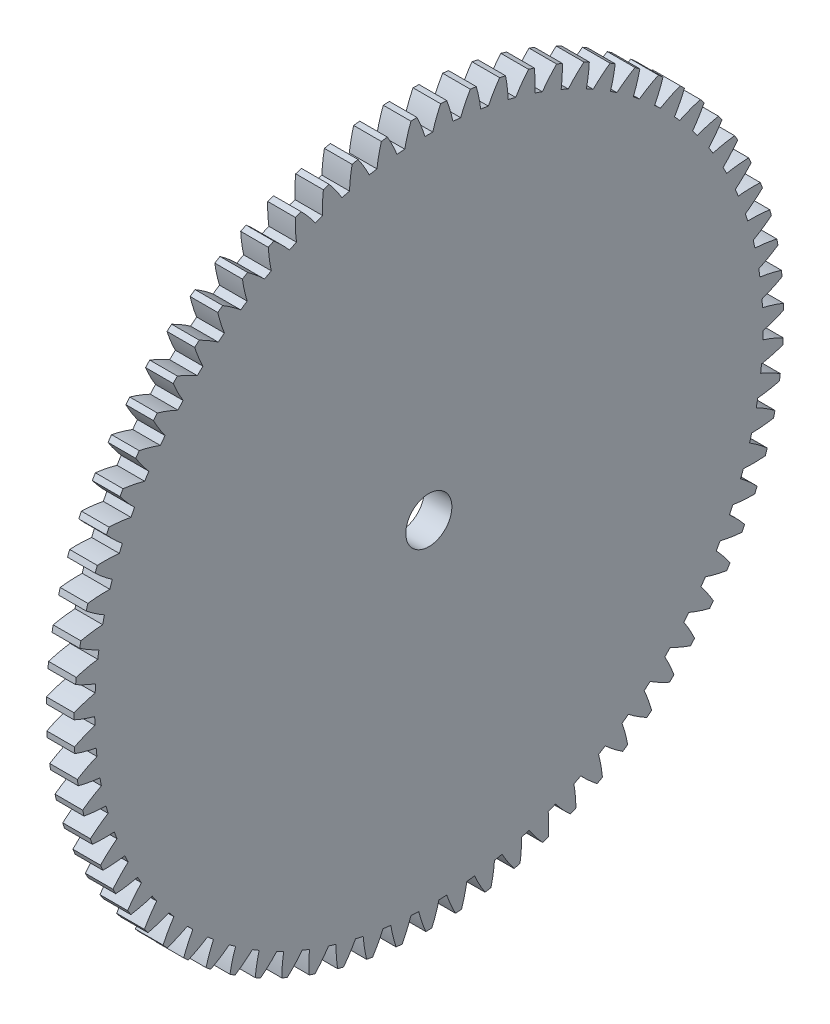
SolidWorks part; units mm, degrees
ref_plane "Plane1" through (0, 0, 0) normal (0, 0, 1) x (1, 0, 0)
ref_plane "Plane2" through (0, 0, 0) normal (0, 1, 0) x (1, 0, 0)
ref_plane "Plane3" through (0, 0, 0) normal (1, 0, 0) x (0, 0, -1)
sketch "HoldingSke" plane through (0, 0, 0) normal (0, 1, 0) x (1, 0, 0)
  line L0 (0, 0) -> (0.2588, -0.9659)
  line L1 (-15, 0) -> (100, 0) construction
  line L2 (0, 0) -> (-2.1039, 2.3779)
  line L3 (0, 0) -> (-11.863, 4.5341)
  line L4 (0, 0) -> (2.2352, 8.3417)
  line L5 (0, 0) -> (-46.8476, -17.4728)
  line L6 (0, 0) -> (-2.4869, -1.6779)
  line L7 (-2.1039, 2.3779) -> (8.6586, 51.2059)
  line L8 (-76.2, 54.61) -> (-75.3, 54.61)
  line L9 (-71.009, 38.7566) -> (-53.1078, 45.2721)
  line L10 (-76.2, 71.12) -> (104.1128, 71.12)
  line L11 (0, 0) -> (-3, 0)
  line L12 (-76.2, 101.6) -> (-76.162, 101.6)
  line L13 (24.9733, 27.94) -> (52.9518, 28.4284)
  line L14 (24.9733, 27.94) -> (24.9743, 27.94)
  line L15 (24.9733, 27.94) -> (100.4006, 29.5858)
  line L16 (-63.627, -1) -> (-12.827, -1)
  circle A0 centre (0, 0) radius 2.5
  circle A1 centre (0, 0) radius 36.249
  circle A2 centre (0, 0) radius 37.5
  circle A3 centre (0, 0) radius 2.5
  dimension "MHD" = 72.498
  dimension "Hub_dia" = 75
  dimension "Bore" = 5
  dimension "MBD" = 5
  dimension "Num_teeth" = 75
  dimension "Pitch_radius" = 180.3128
  dimension "Pitch" = 1
  dimension "Width" = 3
  dimension "Overall_len" = 50
  dimension "Show_teeth" = 75
  dimension "Thickness" = 3
  dimension "OAL" = 50.0001
  dimension "T_dim" = 0.9
  dimension "Ap" = 20
  dimension "H" = 19.05
  dimension "Backlash" = 0.038
  dimension "Addendum_fac" = 1
  dimension "Dedendum_fac" = 1.25
  dimension "Clearance_fac" = 0.25
  dimension "Dedendum_add" = 0.001
  dimension "Module" = 1
sketch "BasProSke" plane through (0, 0, 0) normal (0, 1, 0) x (1, 0, 0)
  line L0 (-10, 0) -> (60, 0) construction
  line L1 (0, 0) -> (0, 38.5)
  line L2 (0, 0) -> (3, 0)
  line L3 (3, 0) -> (3, 38.5)
  line L4 (3, 38.5) -> (0, 38.5)
  dimension "Diameter" = 77
  dimension "Thickness" = 3
revolve "Base-Revolve" add sketch "BasProSke" angle 360 about L0
sketch "TooCutSke" plane through (0, 0, 0) normal (1, 0, 0) x (0, 0, -1)
  line L1 (0, 0) -> (0, 107) construction
  line L2 (0, 0) -> (-0.8518, 37.4903) construction
  line L3 (0, 0) -> (-3.1401, 74.9204) construction
  line L4 (-0.8518, 37.4903) -> (-1.57, 37.4602) construction
  arc A0 (0.4225, 36.2465) -> (-0.4225, 36.2465) centre (0, 0) ccw
  arc A1 (1.296, 38.5036) -> (-1.296, 38.5036) centre (0, 0) ccw
  circle A2 centre (0, 0) radius 37.5 construction
  circle A3 centre (0, 0) radius 35.2385 construction
  arc A4 (-0.4225, 36.2465) -> (-1.296, 38.5036) centre (-14.8025, 31.9787) ccw
  arc A5 (1.296, 38.5036) -> (0.4225, 36.2465) centre (14.8025, 31.9787) ccw
  dimension "Root_dia" = 72.498
  dimension "Overcut_dia" = 77.0508
  dimension "Pitch_dia" = 75
  dimension "Base_dia" = 70.4769
  dimension "Flank_rad" = 15
  dimension "Half_ang" = 2.4
  dimension "Half_CT" = 0.7188
extrude "ToothCut" cut sketch "TooCutSke" along normal through all
fillet "Breaks" [suppressed] radius 0.02
fillet "RootFillets" [suppressed] radius 0.251
pattern_circular "TeethCuts" count 75 every 4.8 about axis through (-10, 0, 0) along (1, 0, 0) of "ToothCut", "RootFillets", "Breaks"
sketch "HubNeaOneSke" plane through (0, 0, 0) normal (-1, 0, 0) x (0, 0, 1)
  circle A0 centre (0, 0) radius 36.249
  dimension "Diameter" = 72.498
extrude "HubNearOne" [suppressed] add sketch "HubNeaOneSke" along normal blind 47.0001
sketch "HubNeaBotSke" plane through (0, 0, 0) normal (-1, 0, 0) x (0, 0, 1)
  circle A0 centre (0, 0) radius 36.249
  dimension "Diameter" = 72.498
extrude "HubNearBoth" [suppressed] add sketch "HubNeaBotSke" along normal blind 23.5
ref_plane "FarPln" through (3, 0, 0) normal (1, 0, 0) x (0, 0, -1)
sketch "HubFarSke" plane through (3, 0, 0) normal (1, 0, 0) x (0, 0, -1)
  circle A0 centre (0, 0) radius 36.249
  dimension "Diameter" = 72.498
extrude "HubFar" [suppressed] add sketch "HubFarSke" along normal blind 23.5
sketch "BorSke" plane through (0, 0, 0) normal (1, 0, 0) x (0, 0, -1)
  circle A0 centre (0, 0) radius 2.5
  dimension "Diameter" = 5
extrude "Bore" cut sketch "BorSke" along normal mid plane 100.0001
sketch "KeySke" plane through (0, 0, 0) normal (1, 0, 0) x (0, 0, -1)
  line L0 (-1, 0) -> (-1, 3.4)
  line L1 (-1, 3.4) -> (1, 3.4)
  line L2 (1, 3.4) -> (1, 0)
  line L3 (0, 0) -> (0, 34) construction
  line L4 (-1, 0) -> (1, 0)
  dimension "Offset" = 3.4
  dimension "Width" = 2
extrude "Keyway" [suppressed] cut sketch "KeySke" along normal mid plane 100.0001
pattern_circular "Keyway2" [suppressed] count 2 every 90 about axis through (-10, 0, 0) along (1, 0, 0)
equation "' \"Module@HoldingSke\" = 6.35"
equation "' \"Num_teeth@HoldingSke\" = 12"
equation "' \"Ap@HoldingSke\" =  20"
equation "' \"Width@HoldingSke\" = 0.5 * 25.4"
equation "' \"Hub_dia@HoldingSke\"= 1 * 25.4"
equation "' \"Overall_len@HoldingSke\" = 1.0 * 25.4"
equation "' \"Bore@HoldingSke\" = 0.75 * 25.4"
equation "' \"T_dim@HoldingSke\" = 0.1 * 25.4"
equation "' \"Width@KeySke\" = 0.25 * 25.4"
equation "' \"Show_teeth@HoldingSke\" = 13"
equation "' \"Backlash@HoldingSke\" = 0.009 * 25.4"
equation "' \"Addendum_fac@HoldingSke\" = 1.0"
equation "' \"Dedendum_fac@HoldingSke\" = 1.25"
equation "' \"Dedendum_add@HoldingSke\" = 0.00005 * 25.4"
equation "' \"Clearance_fac@HoldingSke\" = 0.25"
equation "\"Pitch@HoldingSke\" = 1 / \"Module@HoldingSke\""
equation "\"Overcut_dia@TooCutSke\" = (\"Num_teeth@HoldingSke\" + 2 * \"Addendum_fac@HoldingSke\") / \"Pitch@HoldingSke\" + 0.002 * 25.4"
equation "\"Pitch_dia@TooCutSke\" = \"Num_teeth@HoldingSke\" / \"Pitch@HoldingSke\""
equation "\"Base_dia@TooCutSke\" = \"Num_teeth@HoldingSke\" / \"Pitch@HoldingSke\" * cos((\"Ap@HoldingSke\"  * 3.14159265 / 180))"
equation "\"Root_dia@TooCutSke\" = (\"Num_teeth@HoldingSke\" + 2) / \"Pitch@HoldingSke\" - 2 * (\"Addendum_fac@HoldingSke\" + \"Dedendum_fac@HoldingSke\") / \"Pitch@HoldingSke\" - \"Dedendum_add@HoldingSke\" * 2"
equation "\"Half_ang@TooCutSke\" = 180 / \"Num_teeth@HoldingSke\""
equation "\"Half_CT@TooCutSke\" = \"Num_teeth@HoldingSke\" / \"Pitch@HoldingSke\" * sin((3.14159265 / 2 / \"Num_teeth@HoldingSke\")) / 2 - 7 * \"Backlash@HoldingSke\" / 4"
equation "\"Flank_rad@TooCutSke\" = \"Num_teeth@HoldingSke\" / \"Pitch@HoldingSke\" / 5"
equation "\"Radius@RootFillets\" = \"Clearance_fac@HoldingSke\" / \"Pitch@HoldingSke\" + \"Dedendum_add@HoldingSke\""
equation "\"Break_rad@Breaks\" = 0.02 / \"Pitch@HoldingSke\""
equation "\"Thickness@HoldingSke\" = \"Width@HoldingSke\""
equation "\"OAL@HoldingSke\" = \"Thickness@HoldingSke\""
equation "\"MHD@HoldingSke\" = (\"Num_teeth@HoldingSke\" + 2) / \"Pitch@HoldingSke\" - 2 * (\"Addendum_fac@HoldingSke\" + \"Dedendum_fac@HoldingSke\")  / \"Pitch@HoldingSke\" - \"Dedendum_add@HoldingSke\" * 2"
equation "\"MBD@HoldingSke\" = (\"Num_teeth@HoldingSke\" + 2) / \"Pitch@HoldingSke\" - 2 * (\"Addendum_fac@HoldingSke\" + \"Dedendum_fac@HoldingSke\")  / \"Pitch@HoldingSke\" - \"Dedendum_add@HoldingSke\" * 2 - 0.002 * 25.4"
equation "\"MHD@HoldingSke\" = ((sgn( \"MHD@HoldingSke\" - \"Hub_dia@HoldingSke\" )-1)*( \"MHD@HoldingSke\" - \"Hub_dia@HoldingSke\" ))/-2+ \"Hub_dia@HoldingSke\""
equation "\"MBD@HoldingSke\" = ((sgn( \"MBD@HoldingSke\" - \"Bore@HoldingSke\" )-1)*( \"MBD@HoldingSke\" - \"Bore@HoldingSke\" ))/-2+ \"Bore@HoldingSke\""
equation "\"OAL@HoldingSke\" = ((sgn( \"OAL@HoldingSke\" - \"Overall_len@HoldingSke\" )+1)*( \"OAL@HoldingSke\" - \"Overall_len@HoldingSke\" ))/2 + \"Overall_len@HoldingSke\" + 0.000002 * 25.4"
equation "\"Num_teeth@TeethCuts\" = int( \"Show_teeth@HoldingSke\" ) + 1"
equation "\"Num_teeth@TeethCuts\" = ((sgn( \"Num_teeth@TeethCuts\" - \"Num_teeth@HoldingSke\" )-1)*( \"Num_teeth@TeethCuts\" - \"Num_teeth@HoldingSke\" ))/-2+ \"Num_teeth@HoldingSke\""
equation "\"Num_teeth@TeethCuts\" = ((sgn( \"Num_teeth@TeethCuts\" - 2.0)+1)*( \"Num_teeth@TeethCuts\" - 2.0))/2 +2.0"
equation "\"Angle@TeethCuts\" = 360.0 / \"Num_teeth@HoldingSke\""
equation "\"Diameter@BasProSke\" = (\"Num_teeth@HoldingSke\" + 2 * \"Addendum_fac@HoldingSke\") / \"Pitch@HoldingSke\""
equation "\"Thickness@BasProSke\"  = \"Thickness@HoldingSke\""
equation "' \"Fillet_rad@BasProSke\" =  \"Thickness@HoldingSke\" * 0.05"
equation "\"MHD@HoldingSke\" = ((sgn( \"MHD@HoldingSke\" - \"Root_dia@TooCutSke\" )-1)*( \"MHD@HoldingSke\" - \"Root_dia@TooCutSke\" ))/-2+ \"Root_dia@TooCutSke\""
equation "\"Diameter@HubNeaOneSke\" = \"MHD@HoldingSke\""
equation "\"Length@HubNearOne\" = \"OAL@HoldingSke\" - \"Thickness@BasProSke\""
equation "\"Diameter@HubNeaBotSke\" = \"MHD@HoldingSke\""
equation "\"Length@HubNearBoth\" = ( \"OAL@HoldingSke\" - \"Thickness@BasProSke\" ) / 2.0"
equation "\"Thickness@FarPln\" = \"Thickness@BasProSke\""
equation "\"Diameter@HubFarSke\" = \"MHD@HoldingSke\""
equation "\"Length@HubFar\" = ( \"OAL@HoldingSke\" - \"Thickness@BasProSke\" ) / 2.0"
equation "\"Diameter@BorSke\" = \"MBD@HoldingSke\""
equation "\"D1@Bore\" = \"OAL@HoldingSke\" * 2.0"
equation "\"D1@Keyway\" = \"OAL@HoldingSke\" * 2.0"
equation "\"Offset@KeySke\" = \"T_dim@HoldingSke\" + \"MBD@HoldingSke\" / 2.0"
